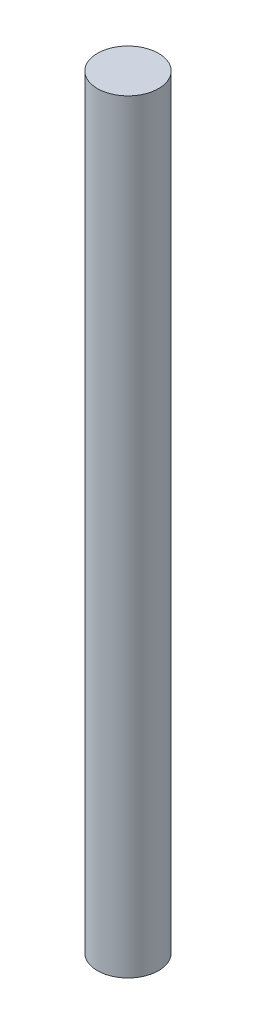
SolidWorks part; units mm, degrees
ref_plane "Front Plane" through (0, 0, 0) normal (0, 0, 1) x (1, 0, 0)
ref_plane "Top Plane" through (0, 0, 0) normal (0, 1, 0) x (1, 0, 0)
ref_plane "Right Plane" through (0, 0, 0) normal (1, 0, 0) x (0, 0, -1)
sketch "Sketch2" plane through (0, 0, 0) normal (0, 1, 0) x (1, 0, 0)
  circle A0 centre (0, 0) radius 20
  dimension "D1" = 40
extrude "Boss-Extrude1" add sketch "Sketch2" along normal blind 500
